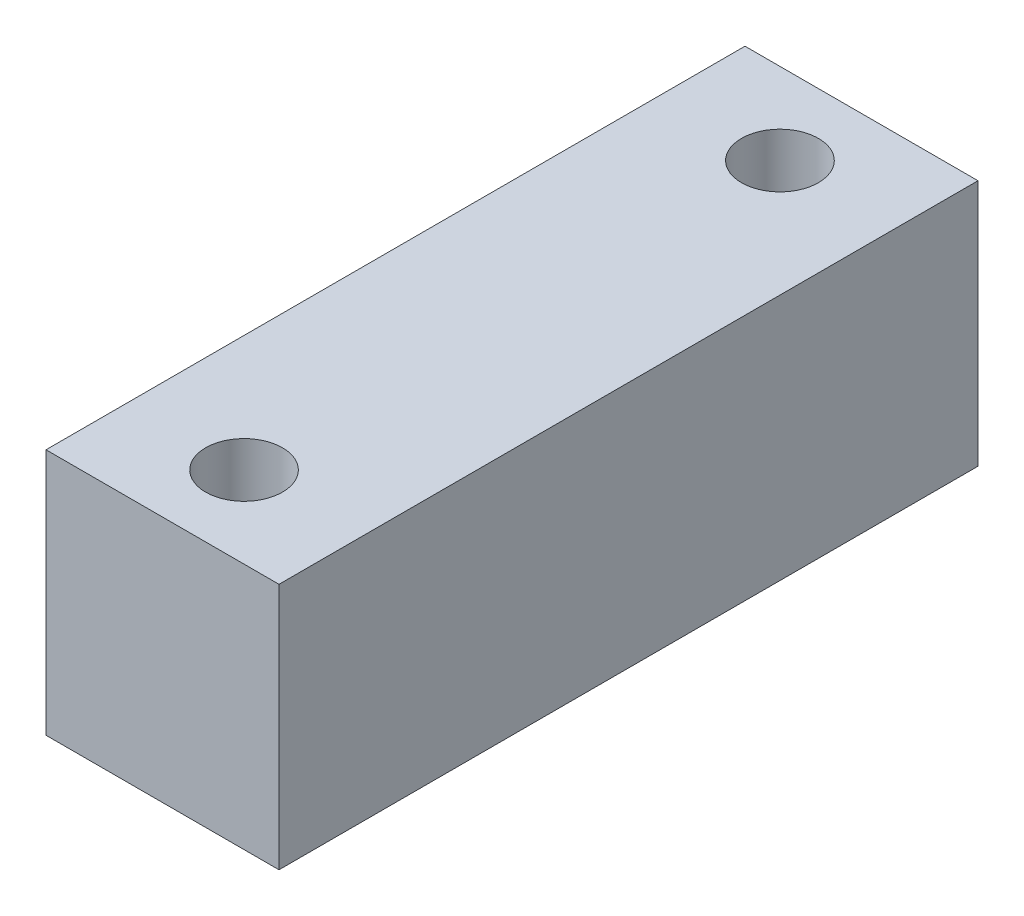
SolidWorks part; units mm, degrees
material "Delrin 2700 NC010, Low Viscosity Acetal Copolymer (SS)"
ref_plane "Front" through (0, 0, 0) normal (0, 0, 1) x (1, 0, 0)
ref_plane "Top" through (0, 0, 0) normal (0, 1, 0) x (1, 0, 0)
ref_plane "Right" through (0, 0, 0) normal (1, 0, 0) x (0, 0, -1)
sketch "Sketch1" plane through (0, 0, 0) normal (0, 1, 0) x (1, 0, 0)
  line B0 (0, -30) -> (-20, -30)
  line B1 (0, -30) -> (0, 30)
  line B2 (0, 30) -> (-20, 30)
  line B3 (-20, -30) -> (-20, 30)
  circle B4 centre (-10, 23) radius 3.3
  circle B5 centre (-10, -23) radius 3.3
sketch_block_instance "Block-BF12 Spacer-1"
sketch_block "Block-BF12 Spacer"
extrude "Boss-Extrude1" add sketch "Sketch1" along normal blind 21.2242
